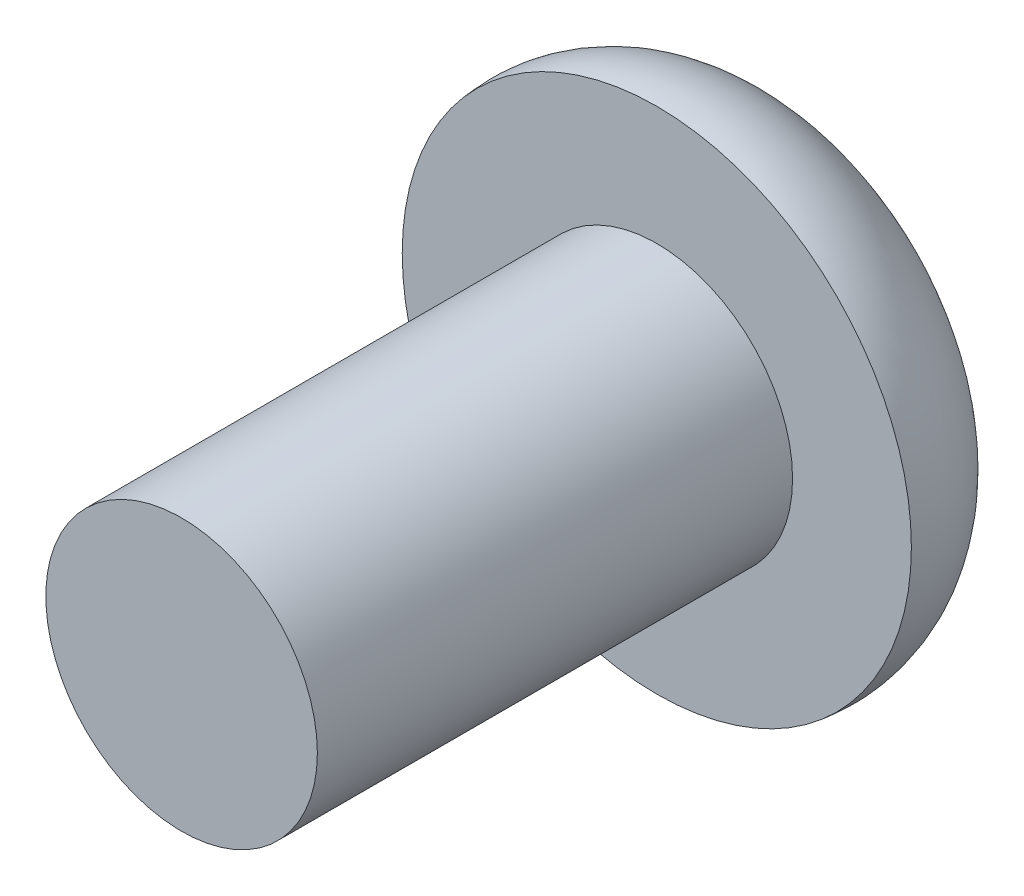
SolidWorks part; units mm, degrees
ref_plane "Front Plane" through (0, 0, 0) normal (0, 0, 1) x (1, 0, 0)
ref_plane "Top Plane" through (0, 0, 0) normal (0, 1, 0) x (1, 0, 0)
ref_plane "Right Plane" through (0, 0, 0) normal (1, 0, 0) x (0, 0, -1)
sketch "Sketch1" plane through (0, 0, 0) normal (0, 1, 0) x (1, 0, 0)
  line L0 (0, 0) -> (0, 9) construction
  line L1 (0, 0) -> (-2, 0)
  line L2 (-2, 0) -> (-2, 7)
  line L3 (-2, 7) -> (-3.75, 7)
  line L4 (-2, 9) -> (0, 9)
  line L5 (0, 0) -> (0, 9)
  arc A0 (-3.75, 7) -> (-2, 9) centre (-2, 7.2344) cw
  dimension "D5" = 2
  dimension "D1" = 2
  dimension "D2" = 3.75
  dimension "D3" = 2
  dimension "D4" = 7
revolve "Revolve1" add sketch "Sketch1" angle 360 about L0
sketch "Sketch2" plane through (0, 0, -9) normal (0, 0, -1) x (-1, 0, 0)
  line L1 (0, -1.4434) -> (1.25, -0.7217)
  line L2 (1.25, -0.7217) -> (1.25, 0.7217)
  line L3 (1.25, 0.7217) -> (0, 1.4434)
  line L4 (0, 1.4434) -> (-1.25, 0.7217)
  line L5 (-1.25, 0.7217) -> (-1.25, -0.7217)
  line L6 (-1.25, -0.7217) -> (0, -1.4434)
  circle A0 centre (0, 0) radius 1.25 construction
  dimension "D1" = 2.5
extrude "Cut-Extrude1" cut sketch "Sketch2" against normal blind 1.8
